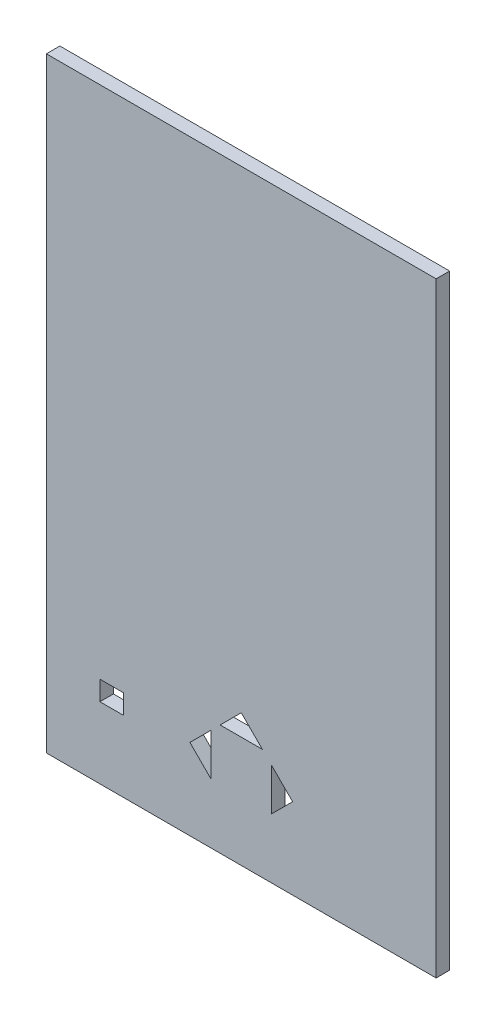
SolidWorks part; units mm, degrees
ref_plane "Front Plane" through (0, 0, 0) normal (0, 0, 1) x (1, 0, 0)
ref_plane "Top Plane" through (0, 0, 0) normal (0, 1, 0) x (1, 0, 0)
ref_plane "Right Plane" through (0, 0, 0) normal (1, 0, 0) x (0, 0, -1)
sketch "Sketch1" plane through (0, 0, 0) normal (0, 0, 1) x (1, 0, 0)
  line L0 (-92.075, -142.875) -> (92.075, -142.875) construction
  line L1 (-92.075, 142.875) -> (-92.075, -142.875) construction
  line L2 (92.075, 142.875) -> (-92.075, 142.875) construction
  line L3 (92.075, -142.875) -> (92.075, 142.875) construction
  line L4 (-92.075, -142.875) -> (92.075, -142.875) construction
  line L5 (-92.075, 142.875) -> (-92.075, -142.875) construction
  line L6 (92.075, 142.875) -> (-92.075, 142.875) construction
  line L7 (92.075, -142.875) -> (92.075, 142.875) construction
  line L8 (-91.7625, -142.5625) -> (91.7625, -142.5625)
  line L9 (91.7625, -142.5625) -> (91.7625, 142.5625)
  line L10 (91.7625, 142.5625) -> (-91.7625, 142.5625)
  line L11 (-91.7625, 142.5625) -> (-91.7625, -142.5625)
  dimension "D1" = 0.3125
extrude "Boss-Extrude1" add sketch "Sketch1" against normal blind 6.35
sketch "Sketch2" plane through (0, 0, 0) normal (0, 0, 1) x (1, 0, 0)
  line L0 (0, 0) -> (0, -142.5625) construction
  line L1 (-91.7625, -142.5625) -> (91.7625, -142.5625) construction
  line L2 (14.6369, -95.4822) -> (14.6369, -113.4428) construction
  line L3 (14.6369, -113.4428) -> (23.6172, -104.4625) construction
  line L4 (23.6172, -104.4625) -> (14.6369, -95.4822) construction
  line L5 (23.6172, -104.4625) -> (14.6369, -104.4625) construction
  line L6 (24.1829, -104.4625) -> (14.2369, -94.5166)
  line L7 (14.2369, -94.5166) -> (14.2369, -114.4084)
  line L8 (14.2369, -114.4084) -> (24.1829, -104.4625)
  line L9 (0, -80.2796) -> (-9.9459, -90.2256)
  line L10 (-9.9459, -90.2256) -> (9.9459, -90.2256)
  line L11 (9.9459, -90.2256) -> (0, -80.2796)
  line L12 (-8.9803, -89.8256) -> (8.9803, -89.8256) construction
  line L13 (8.9803, -89.8256) -> (0, -80.8453) construction
  line L14 (0, -80.8453) -> (-8.9803, -89.8256) construction
  line L15 (0, -80.8453) -> (0, -89.8256) construction
  line L16 (-24.1829, -104.4625) -> (-14.2369, -114.4084)
  line L17 (-14.2369, -114.4084) -> (-14.2369, -94.5166)
  line L18 (-14.2369, -94.5166) -> (-24.1829, -104.4625)
  line L19 (-14.6369, -113.4428) -> (-14.6369, -95.4822) construction
  line L20 (-14.6369, -95.4822) -> (-23.6172, -104.4625) construction
  line L21 (-23.6172, -104.4625) -> (-14.6369, -113.4428) construction
  line L22 (-23.6172, -104.4625) -> (-14.6369, -104.4625) construction
  line L23 (0, -104.4625) -> (14.6369, -104.4625) construction
  line L24 (0, -104.4625) -> (0, -89.8256) construction
  line L26 (-55.36, -99.8625) -> (-66.56, -99.8625)
  line L27 (-55.36, -99.8625) -> (-55.36, -109.0625)
  line L28 (-55.36, -109.0625) -> (-66.56, -109.0625)
  line L29 (-66.56, -99.8625) -> (-66.56, -109.0625)
  line L30 (-55.36, -99.8625) -> (-66.56, -109.0625) construction
  line L31 (-55.36, -109.0625) -> (-66.56, -99.8625) construction
  line L39 (-91.7625, 142.5625) -> (-91.7625, -142.5625)
  line L40 (-91.7625, -142.5625) -> (91.7625, -142.5625)
  line L41 (91.7625, -142.5625) -> (91.7625, 142.5625)
  line L42 (91.7625, 142.5625) -> (-91.7625, 142.5625)
  line L43 (-91.7625, 142.5625) -> (-91.7625, -142.5625) construction
  line L44 (-91.7625, -142.5625) -> (91.7625, -142.5625) construction
  line L45 (91.7625, -142.5625) -> (91.7625, 142.5625) construction
  line L46 (91.7625, 142.5625) -> (-91.7625, 142.5625) construction
  point P10 (17.78, -104.4625)
  point P11 (0, -104.4625)
  point P20 (0, -86.6825)
  point P28 (-17.78, -104.4625)
  point P35 (-60.96, -104.4625)
  dimension "D1" = 12.7
  dimension "D2" = 8.9803
  dimension "D3" = 3.1431
  dimension "D4" = 35.56
  dimension "D7" = 90
  dimension "D8" = 38.1
  dimension "D9" = 11.2
  dimension "D10" = 9.2
  dimension "D11" = 60.96
  dimension "D13" = 285.125
  dimension "D5" = 0.4
  dimension "D12" = 0
  dimension "D6" = 3
extrude "Cut-Extrude1" cut sketch "Sketch2" against normal through all
equation "\"D3@Sketch2\"=7/20*\"D2@Sketch2\""
equation "\"D9@Sketch2\"=11mm+.2mm"
equation "\"D10@Sketch2\"=9mm+.2mm"
